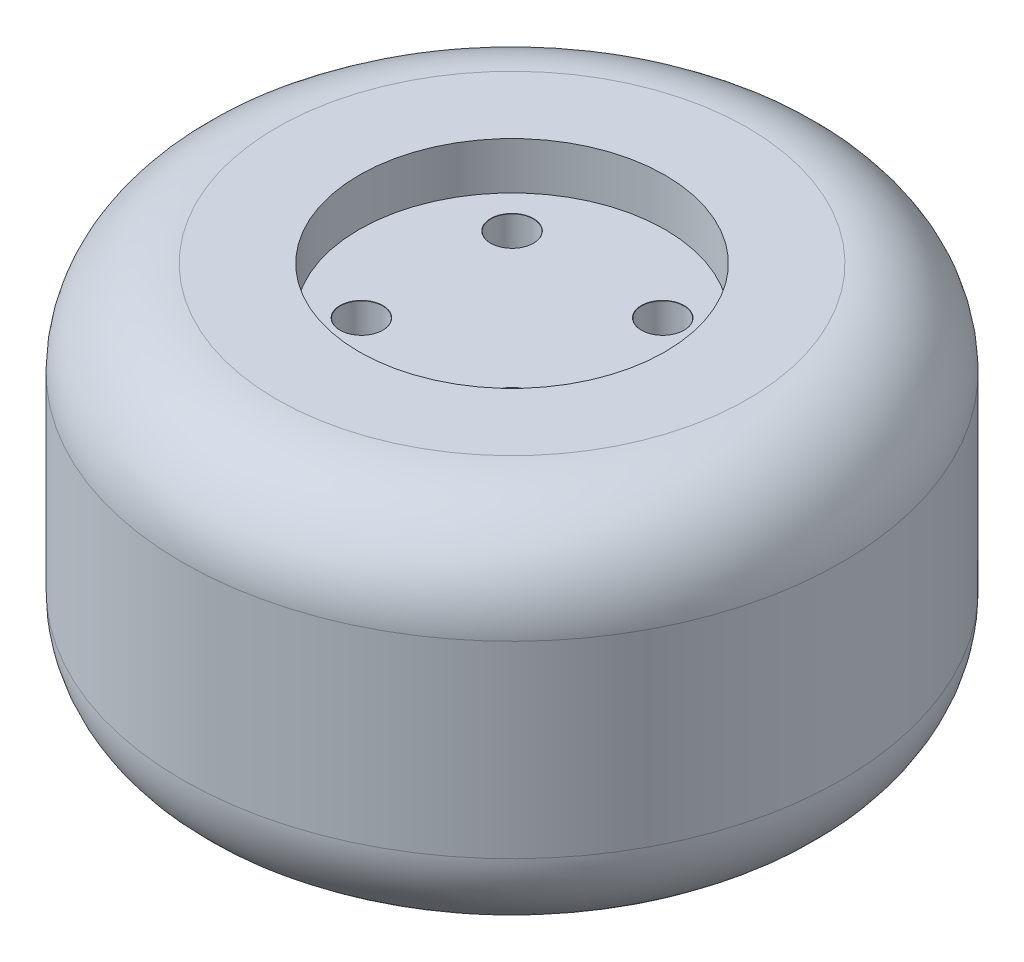
SolidWorks part; units mm, degrees
ref_plane "Front Plane" through (0, 0, 0) normal (0, 0, 1) x (1, 0, 0)
ref_plane "Top Plane" through (0, 0, 0) normal (0, 1, 0) x (1, 0, 0)
ref_plane "Right Plane" through (0, 0, 0) normal (1, 0, 0) x (0, 0, -1)
sketch "Sketch1" plane through (0, 0, 0) normal (0, 1, 0) x (1, 0, 0)
  circle A0 centre (0, 0) radius 35
  dimension "D1" = 70
extrude "Boss-Extrude1" add sketch "Sketch1" along normal blind 40
sketch "Sketch2" plane through (0, 40, 0) normal (0, 1, 0) x (1, 0, 0)
  circle A0 centre (0, 0) radius 16.25
  dimension "D1" = 32.5
extrude "Cut-Extrude1" cut sketch "Sketch2" against normal blind 5
hole_wizard "M4 Clearance Hole1" positions "Sketch5" profile "Sketch4" hole size "M4" standard "ANSI Metric"
sketch "Sketch5" plane through (0, 35, 0) normal (0, 1, 0) x (1, 0, 0)
  point P0 (-8, 8)
  point P2 (8, 8)
  point P4 (8, -8)
  point P6 (-8, -8)
  dimension "D1" = 8
  dimension "D2" = 8
  dimension "D3" = 8
  dimension "D4" = 8
  dimension "D5" = 8
sketch "Sketch4" plane through (-8, 35, -8) normal (1, 0, 0) x (0, 0, 1)
  line L0 (0, 0) -> (0, 14.3519)
  line L1 (0, 14.3519) -> (2.25, 13)
  line L2 (2.25, 13) -> (2.25, 0.025)
  line L3 (2.25, 0.025) -> (2.275, 0)
  line L5 (2.275, 0) -> (0, 0)
  line L6 (-2.25, 0.025) -> (-2.275, 0) construction
  line L10 (0, 14.3519) -> (-2.25, 13) construction
  line L11 (0, -6.35) -> (0, 107.95) construction
  dimension "Hole Dia." = 4.5
  dimension "Hole Depth" = 13
  dimension "Near C'Sink Dia." = 4.55
  dimension "Near C'Sink Angle" = 90
  dimension "Drill Angle" = 118
fillet "Fillet4" radius 10 2 edges at (0, 0, 35) (0, 40, 35)
